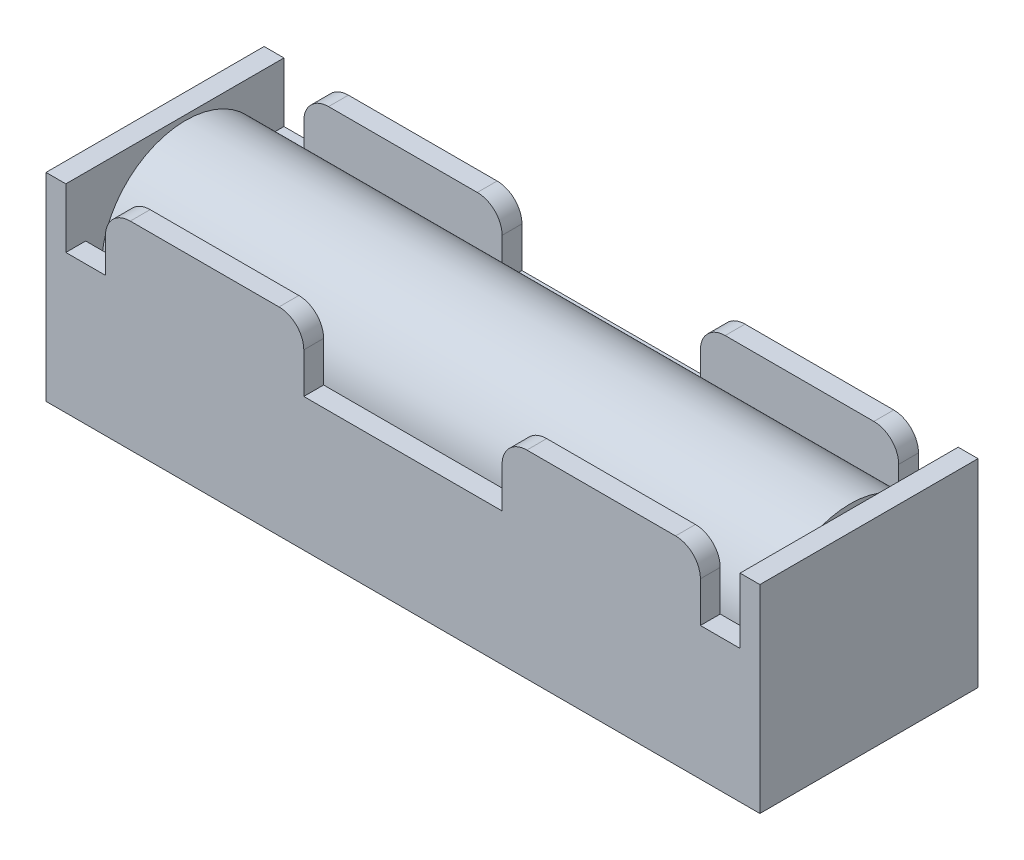
SolidWorks part; units mm, degrees
ref_plane "Front Plane" through (0, 0, 0) normal (0, 0, 1) x (1, 0, 0)
ref_plane "Top Plane" through (0, 0, 0) normal (0, 1, 0) x (1, 0, 0)
ref_plane "Right Plane" through (0, 0, 0) normal (1, 0, 0) x (0, 0, -1)
sketch "Sketch1" plane through (0, 0, 0) normal (0, 1, 0) x (1, 0, 0)
  line L1 (-48.3887, 23.7571) -> (23.6113, 23.7571)
  line L2 (-48.3887, 23.7571) -> (-48.3887, 1.7571)
  line L3 (-48.3887, 1.7571) -> (23.6113, 1.7571)
  line L4 (23.6113, 23.7571) -> (23.6113, 1.7571)
  dimension "D1" = 72
  dimension "D2" = 22
extrude "Boss-Extrude1" add sketch "Sketch1" along normal blind 20
sketch "Sketch2" plane through (0, 20, 0) normal (0, 1, 0) x (1, 0, 0)
  line L0 (-48.3887, 23.7571) -> (-48.3887, 1.7571) construction
  line L1 (-46.3887, 21.7571) -> (21.6113, 21.7571)
  line L2 (-46.3887, 21.7571) -> (-46.3887, 3.7571)
  line L3 (-46.3887, 3.7571) -> (21.6113, 3.7571)
  line L4 (21.6113, 21.7571) -> (21.6113, 3.7571)
  line L5 (23.6113, 23.7571) -> (-48.3887, 23.7571) construction
  line L6 (23.6113, 1.7571) -> (23.6113, 23.7571) construction
  line L7 (-48.3887, 1.7571) -> (23.6113, 1.7571) construction
  point P8 (23.6113, 12.7571)
  dimension "D1" = 2
  dimension "D2" = 2
  dimension "D3" = 2
  dimension "D4" = 2
extrude "Cut-Extrude1" cut sketch "Sketch2" against normal blind 18
sketch "Sketch4" plane through (0, 0, -1.7571) normal (0, 0, 1) x (1, 0, 0)
  line L0 (-46.3887, 14.007) -> (-42.388, 14.007)
  line L1 (-48.3887, 20) -> (-48.3887, 0) construction
  line L2 (-42.388, 14.007) -> (-42.388, 17.5)
  line L3 (21.6113, 20) -> (-46.3887, 20)
  line L4 (-39.888, 20) -> (-24.888, 20)
  line L5 (-22.3887, 17.5007) -> (-22.3887, 13.4296)
  line L6 (-22.3887, 13.4296) -> (-2.3887, 13.4296)
  line L7 (-2.3887, 13.4296) -> (-2.3887, 17.5)
  line L8 (0.1113, 20) -> (15.1113, 20)
  line L9 (17.6113, 17.5) -> (17.6113, 13.4242)
  line L10 (17.6113, 13.4242) -> (21.6113, 13.4242)
  line L11 (23.6113, 20) -> (23.6113, 0) construction
  line L12 (23.6113, 13.4242) -> (23.6113, 20)
  line L13 (15.1113, 20) -> (0.1113, 20)
  line L14 (-46.3887, 20) -> (-46.3887, 14.007)
  line L15 (-24.888, 20) -> (-39.888, 20)
  line L16 (-48.3887, 20) -> (23.6113, 20) construction
  line L17 (21.6113, 13.4242) -> (21.6113, 20)
  arc A0 (-39.888, 20) -> (-42.388, 17.5) centre (-39.888, 17.5) ccw
  arc A1 (-22.3887, 17.5007) -> (-24.888, 20) centre (-24.888, 17.5007) ccw
  arc A2 (0.1113, 20) -> (-2.3887, 17.5) centre (0.1113, 17.5) ccw
  arc A3 (17.6113, 17.5) -> (15.1113, 20) centre (15.1113, 17.5) ccw
  line M3 (23.6113, 20) -> (-48.3887, 20)
  dimension "D1" = 5
  dimension "D2" = 4.9986
  dimension "D3" = 5
  dimension "D4" = 5
  dimension "D5" = 20
  dimension "D6" = 15
  dimension "D7" = 15
  dimension "D8" = 2
  dimension "D9" = 2
  dimension "D10" = 4.0007
extrude "Cut-Extrude2" cut sketch "Sketch4" against normal blind 30 contours A0 L14 L0 L2 M3 | A2 A1 L5 L6 L7 M3 | A3 L9 L10 L17 M3
sketch "Sketch5" plane through (21.6113, 0, 0) normal (-1, 0, 0) x (0, 0, 1)
  line L0 (-23.7571, 20) -> (-1.7571, 20) construction
  circle A0 centre (-12.8599, 12) radius 8.5
  dimension "D1" = 17
  dimension "D2" = 8
extrude "Boss-Extrude3" add sketch "Sketch5" along normal blind 67
sketch "Sketch6" plane through (21.6113, 0, 0) normal (-1, 0, 0) x (0, 0, 1)
  line L0 (-23.7571, 20) -> (-1.7571, 20) construction
  circle A0 centre (-13.0348, 12) radius 8.5
  dimension "D1" = 17
  dimension "D2" = 8
